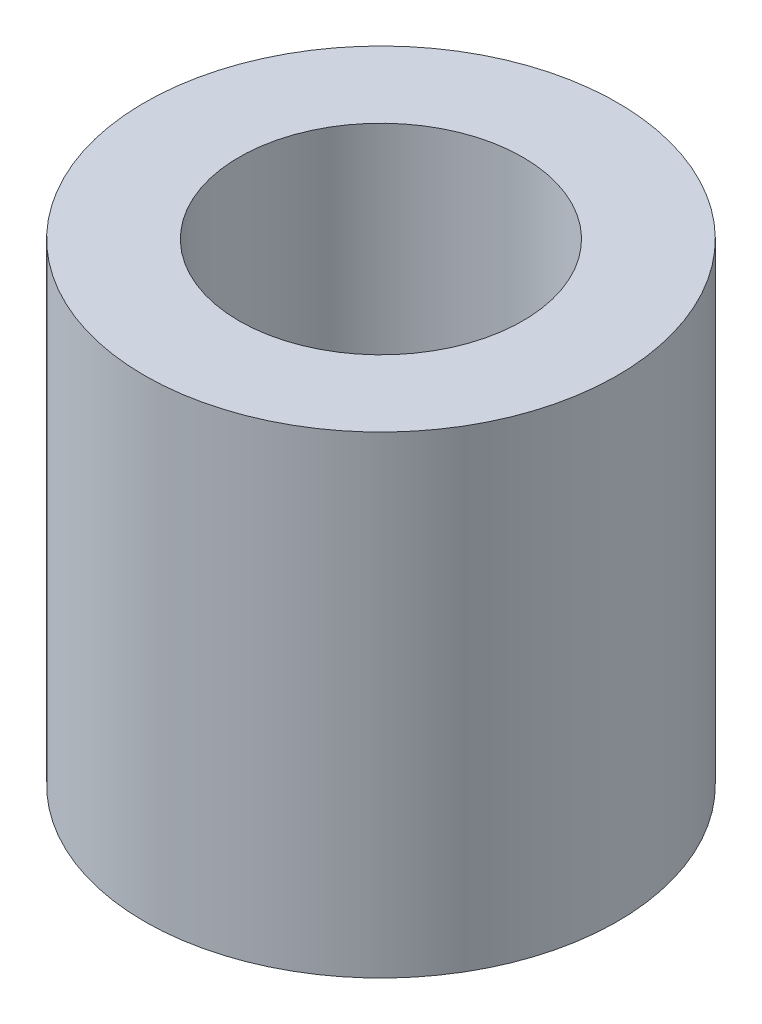
SolidWorks part; units mm, degrees
ref_plane "前视基准面" through (0, 0, 0) normal (0, 0, 1) x (1, 0, 0)
ref_plane "上视基准面" through (0, 0, 0) normal (0, 1, 0) x (1, 0, 0)
ref_plane "右视基准面" through (0, 0, 0) normal (1, 0, 0) x (0, 0, -1)
sketch "草图1" plane through (0, 0, 0) normal (0, 1, 0) x (1, 0, 0)
  circle A0 centre (0, 0) radius 1.5
  circle A1 centre (0, 0) radius 2.5
  dimension "D1" = 5
  dimension "D2" = 3
extrude "凸台-拉伸1" add sketch "草图1" along normal blind 5
